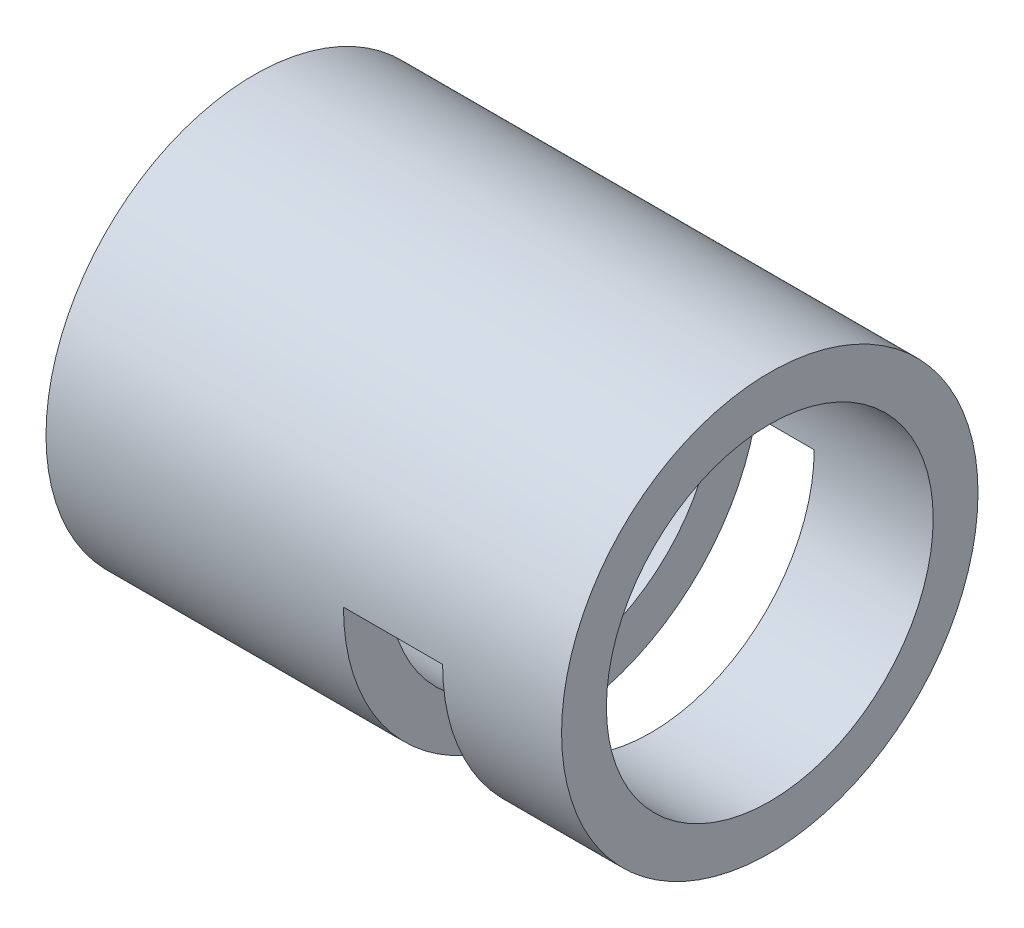
SolidWorks part; units mm, degrees
ref_plane "Front Plane" through (0, 0, 0) normal (0, 0, 1) x (1, 0, 0)
ref_plane "Top Plane" through (0, 0, 0) normal (0, 1, 0) x (1, 0, 0)
ref_plane "Right Plane" through (0, 0, 0) normal (1, 0, 0) x (0, 0, -1)
sketch "Sketch1" plane through (0, 0, 0) normal (1, 0, 0) x (0, 0, -1)
  circle A0 centre (0, 0) radius 13.335
  circle A1 centre (0, 0) radius 10.4648
  dimension "D1" = 26.67
  dimension "D2" = 20.9296
extrude "Boss-Extrude1" add sketch "Sketch1" along normal blind 33.02
sketch "Sketch2" plane through (0, 0, 0) normal (0, 0, 1) x (1, 0, 0)
  line L1 (19.05, -13.335) -> (25.4, -13.335)
  line L2 (19.05, -13.335) -> (19.05, 0)
  line L3 (19.05, 0) -> (25.4, 0)
  line L4 (25.4, -13.335) -> (25.4, 0)
  line L5 (55, 0) -> (-55, 0) construction
  line L6 (0, -13.335) -> (33.02, -13.335) construction
  line L7 (33.02, -13.335) -> (33.02, 13.335) construction
  dimension "D1" = 7.62
  dimension "D2" = 6.35
extrude "Cut-Extrude1" cut sketch "Sketch2" against normal through all both and the other way through all
